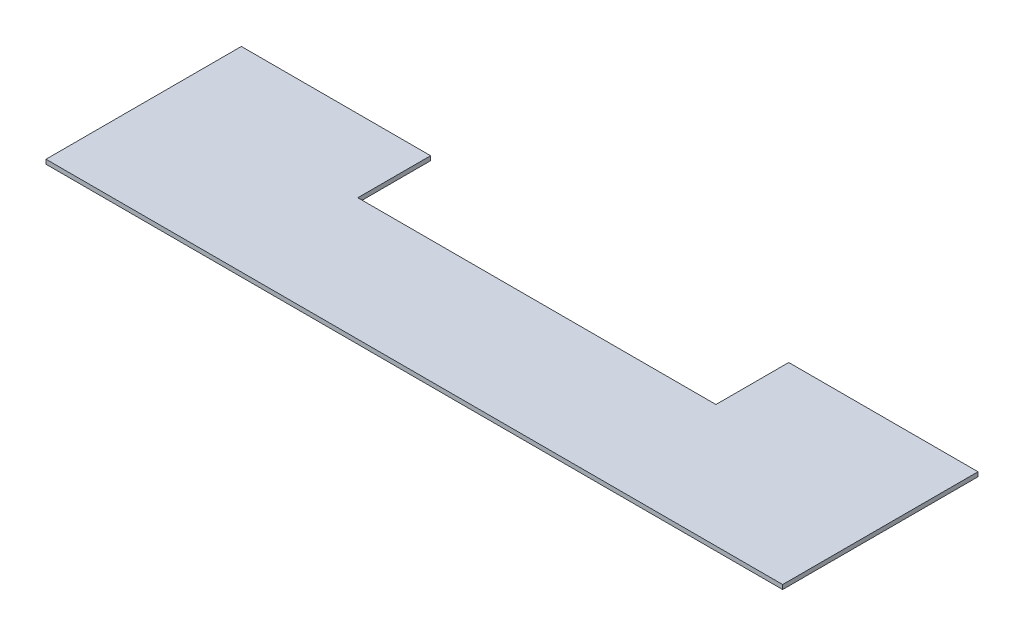
SolidWorks part; units mm, degrees
ref_plane "Front Plane" through (0, 0, 0) normal (0, 0, 1) x (1, 0, 0)
ref_plane "Top Plane" through (0, 0, 0) normal (0, 1, 0) x (1, 0, 0)
ref_plane "Right Plane" through (0, 0, 0) normal (1, 0, 0) x (0, 0, -1)
sketch "Sketch1" plane through (0, 0, 0) normal (0, 1, 0) x (1, 0, 0)
  line L0 (-297.3337, 57.5536) -> (-167.3337, 57.5536)
  line L1 (-167.3337, 57.5536) -> (-167.3337, 17.5536)
  line L2 (208.6663, 57.5536) -> (78.6663, 57.5536)
  line L3 (78.6663, 57.5536) -> (78.6663, 17.5536)
  line L5 (-297.3337, 57.5536) -> (-297.3337, -76.6274)
  line L6 (-297.3337, -76.6274) -> (208.6663, -76.6274)
  line L7 (208.6663, -76.6274) -> (208.6663, 57.5536)
  line L8 (-167.3337, 17.5536) -> (-167.3337, 7.5536)
  line L9 (-167.3337, 7.5536) -> (78.6663, 7.5536)
  line L10 (78.6663, 7.5536) -> (78.6663, 17.5536)
extrude "Boss-Extrude1" add sketch "Sketch1" along normal blind 3
